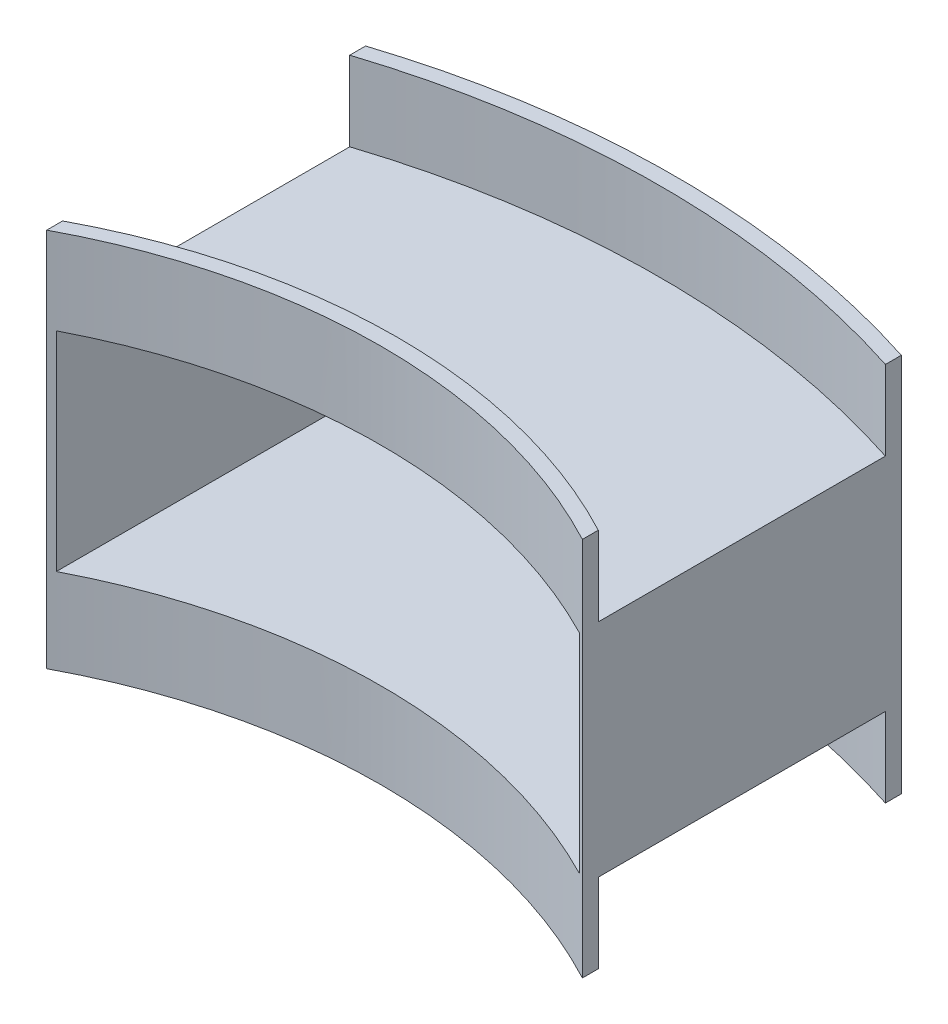
SolidWorks part; units mm, degrees
ref_plane "Front Plane" through (0, 0, 0) normal (0, 0, 1) x (1, 0, 0)
ref_plane "Top Plane" through (0, 0, 0) normal (0, 1, 0) x (1, 0, 0)
ref_plane "Right Plane" through (0, 0, 0) normal (1, 0, 0) x (0, 0, -1)
sketch "Sketch1" plane through (0, 0, 0) normal (0, 0, 1) x (1, 0, 0)
  line L1 (-16.473, -6.565) -> (16.473, -6.565)
  line L2 (-16.473, -6.565) -> (-16.473, 6.565)
  line L3 (-16.473, 6.565) -> (16.473, 6.565)
  line L4 (16.473, -6.565) -> (16.473, 6.565)
  line L5 (-16.473, -6.565) -> (16.473, 6.565) construction
  line L6 (-16.473, 6.565) -> (16.473, -6.565) construction
  line L7 (-16.873, -6.965) -> (16.873, -6.965)
  line L8 (-16.873, -6.965) -> (-16.873, 6.965)
  line L9 (-16.873, 6.965) -> (16.873, 6.965)
  line L10 (16.873, -6.965) -> (16.873, 6.965)
  line L11 (-16.873, -6.965) -> (16.873, 6.965) construction
  line L12 (-16.873, 6.965) -> (16.873, -6.965) construction
  point P0 (0, 0)
  point P6 (0, 0)
  dimension "D1" = 32.946
  dimension "D2" = 13.13
  dimension "D3" = 0.4
  dimension "D4" = 0.4
extrude "Boss-Extrude1" add sketch "Sketch1" along normal mid plane 22.74
sketch "Sketch3" plane through (0, 6.965, 0) normal (0, 1, 0) x (1, 0, 0)
  line L0 (16.873, 8.7179) -> (-16.873, 8.7179)
  line L1 (16.873, -11.37) -> (16.873, 11.37) construction
  line L2 (-16.873, -11.37) -> (-16.873, 11.37) construction
  line L3 (16.873, 11.37) -> (-16.873, 11.37) construction
  line L7 (16.873, -7.171) -> (-16.873, -7.171)
  line L8 (16.873, -11.37) -> (-16.873, -11.37)
  arc A0 (-16.873, 8.7179) -> (16.873, 8.7179) centre (0, -43.63) cw
  arc A1 (16.873, -11.37) -> (-16.873, -11.37) centre (0, -43.171) ccw
  dimension "D1" = 55
  dimension "D2" = 36
extrude "Cut-Extrude1" cut sketch "Sketch3" against normal through all
sketch "Sketch4" plane through (0, 6.965, 0) normal (0, 1, 0) x (1, 0, 0)
  line L0 (-16.873, -11.37) -> (-16.873, -10.37)
  line L1 (-16.873, -11.37) -> (-16.873, 8.7179) construction
  line L2 (16.873, -11.37) -> (16.873, -10.37)
  line L3 (16.873, -11.37) -> (16.873, 8.7179) construction
  line L4 (-16.873, 8.7179) -> (-16.873, 7.7179)
  line L5 (16.873, 8.7179) -> (16.873, 7.7179)
  arc A0 (-16.873, -11.37) -> (16.873, -11.37) centre (0, -43.171) cw
  arc A1 (-16.873, -10.37) -> (16.873, -10.37) centre (0, -42.171) cw
  arc A2 (-16.873, 8.7179) -> (16.873, 8.7179) centre (0, -43.63) cw
  arc A3 (-16.873, 7.7179) -> (16.873, 7.7179) centre (0, -44.63) cw
  dimension "D3" = 36
  dimension "D4" = 36
  dimension "D7" = 55
  dimension "D8" = 55
  dimension "D1" = 1
  dimension "D2" = 1
  dimension "D5" = 1
  dimension "D6" = 1
extrude "Boss-Extrude2" add sketch "Sketch4" along normal blind 5
sketch "Sketch5" plane through (0, -6.965, 0) normal (0, -1, 0) x (1, 0, 0)
  line L0 (-16.873, 11.37) -> (-16.873, 10.37)
  line L1 (-16.873, 11.37) -> (-16.873, -8.7179) construction
  line L2 (16.873, 11.37) -> (16.873, 10.37)
  line L3 (16.873, 11.37) -> (16.873, -8.7179) construction
  line L4 (-16.873, -8.7179) -> (-16.873, -7.7179)
  line L5 (16.873, -8.7179) -> (16.873, -7.7179)
  arc A0 (-16.873, 11.37) -> (16.873, 11.37) centre (0, 43.171) ccw
  arc A1 (-16.873, 10.37) -> (16.873, 10.37) centre (0, 42.171) ccw
  arc A2 (-16.873, -8.7179) -> (16.873, -8.7179) centre (0, 43.63) ccw
  arc A3 (-16.873, -7.7179) -> (16.873, -7.7179) centre (0, 44.63) ccw
  dimension "D3" = 36
  dimension "D4" = 36
  dimension "D7" = 55
  dimension "D8" = 55
  dimension "D1" = 1
  dimension "D2" = 1
  dimension "D5" = 1
  dimension "D6" = 1
extrude "Boss-Extrude3" add sketch "Sketch5" along normal blind 5
